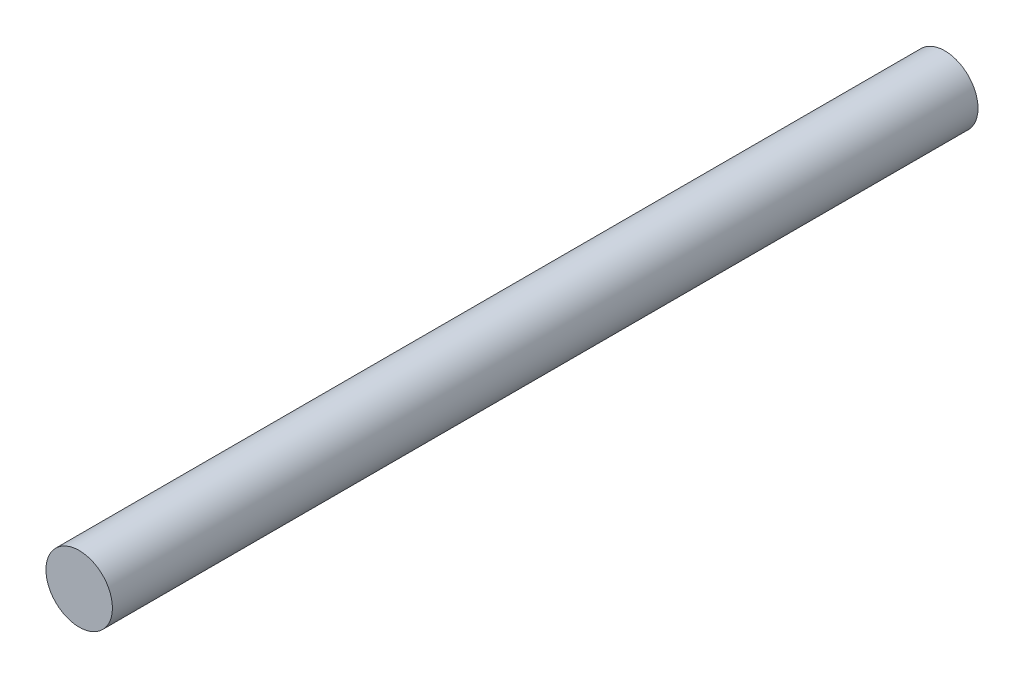
SolidWorks part; units mm, degrees
ref_plane "Front Plane" through (0, 0, 0) normal (0, 0, 1) x (1, 0, 0)
ref_plane "Top Plane" through (0, 0, 0) normal (0, 1, 0) x (1, 0, 0)
ref_plane "Right Plane" through (0, 0, 0) normal (1, 0, 0) x (0, 0, -1)
sketch "Sketch1" plane through (0, 0, 0) normal (0, 0, 1) x (1, 0, 0)
  circle A0 centre (0, 0) radius 3.175
  dimension "D1" = 6.35
extrude "Boss-Extrude1" add sketch "Sketch1" against normal blind 82.677 contours A0
